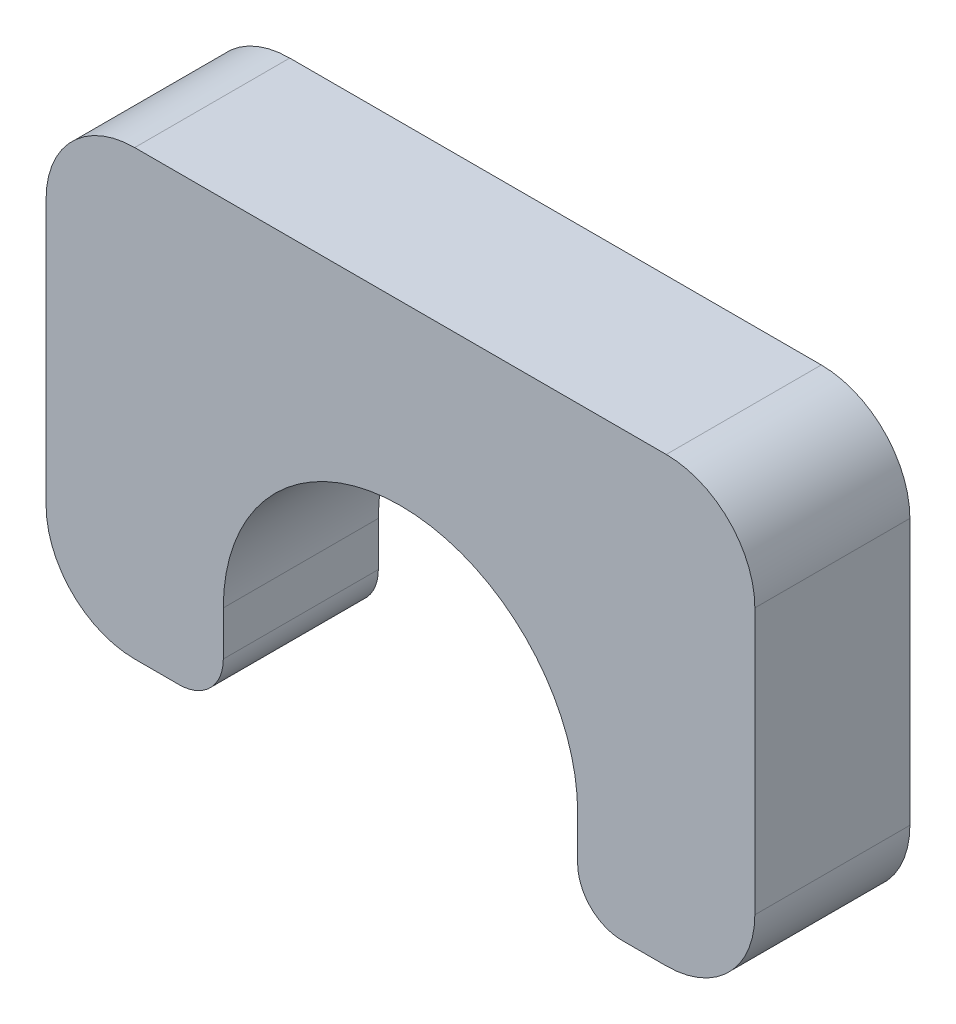
SolidWorks part; units mm, degrees
material "AISI 316 Stainless Steel Sheet (SS)"
ref_plane "Front Plane" through (0, 0, 0) normal (0, 0, 1) x (1, 0, 0)
ref_plane "Top Plane" through (0, 0, 0) normal (0, 1, 0) x (1, 0, 0)
ref_plane "Right Plane" through (0, 0, 0) normal (1, 0, 0) x (0, 0, -1)
sketch "Sketch1" plane through (0, 0, 0) normal (0, 0, 1) x (1, 0, 0)
  line L0 (-4, -5) -> (-4, -3)
  line L1 (-6, -5) -> (6, -5)
  line L2 (-8, -3) -> (-8, 3)
  line L3 (-6, 5) -> (6, 5)
  line L4 (8, -3) -> (8, 3)
  line L5 (-8, -5) -> (8, 5) construction
  line L6 (-8, 5) -> (8, -5) construction
  line L9 (4, -5) -> (4, -3)
  arc A0 (-6, -5) -> (-8, -3) centre (-6, -3) cw
  arc A1 (6, -5) -> (8, -3) centre (6, -3) ccw
  arc A2 (6, 5) -> (8, 3) centre (6, 3) cw
  arc A3 (-8, 3) -> (-6, 5) centre (-6, 3) cw
  arc A6 (-4, -3) -> (4, -3) centre (0, -3) cw
  point P0 (0, 0)
  point P22 (0, -5)
  dimension "D3" = 2
  dimension "D4" = 2
  dimension "D1" = 16
  dimension "D2" = 10
  dimension "D5" = 2
  dimension "D6" = 4
  dimension "D7" = 4
extrude "Boss-Extrude1" add sketch "Sketch1" along normal blind 3.5 contours L0 A6 L9 L1 A1 L4 A2 L3 A3 L2 A0
fillet "Fillet1" radius 1 2 edges at (4, -5, 1.75) (-4, -5, 1.75)
